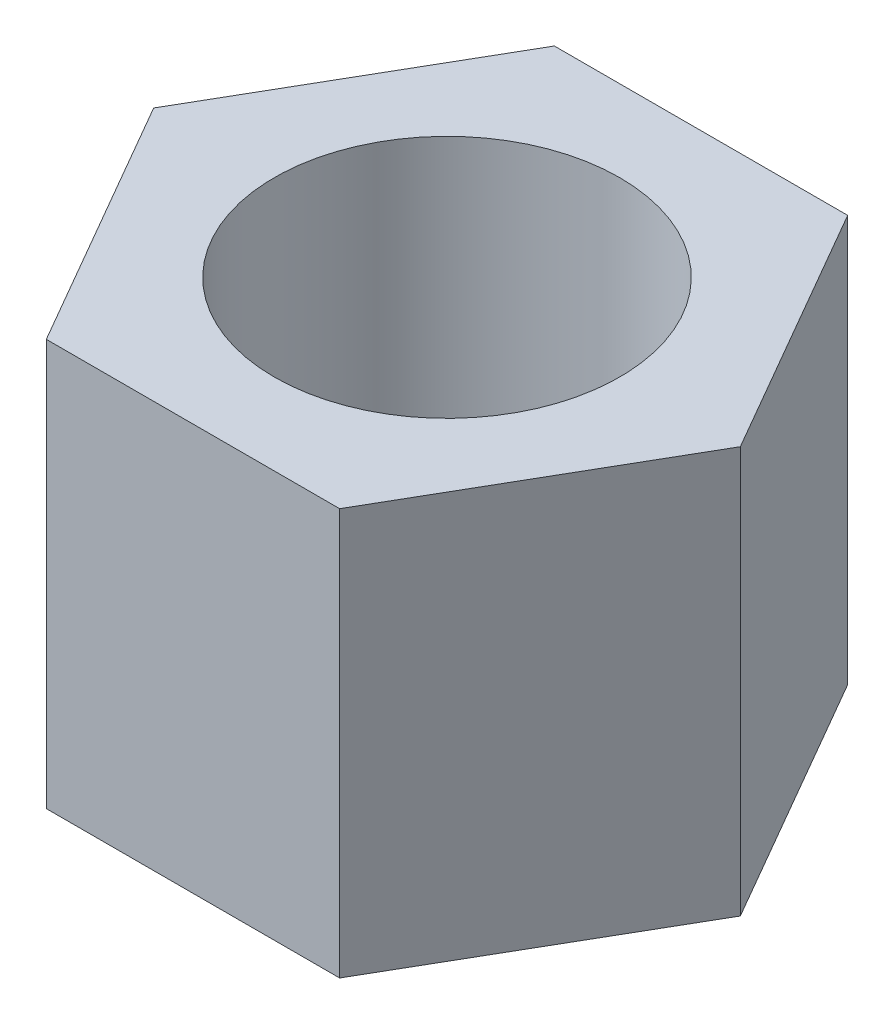
SolidWorks part; units mm, degrees
ref_plane "Front Plane" through (0, 0, 0) normal (0, 0, 1) x (1, 0, 0)
ref_plane "Top Plane" through (0, 0, 0) normal (0, 1, 0) x (1, 0, 0)
ref_plane "Right Plane" through (0, 0, 0) normal (1, 0, 0) x (0, 0, -1)
sketch "Sketch1" plane through (0, 0, 0) normal (0, 1, 0) x (1, 0, 0)
  line L1 (-2.8868, 0) -> (-1.4434, -2.5)
  line L2 (-1.4434, -2.5) -> (1.4434, -2.5)
  line L3 (1.4434, -2.5) -> (2.8868, 0)
  line L4 (2.8868, 0) -> (1.4434, 2.5)
  line L5 (1.4434, 2.5) -> (-1.4434, 2.5)
  line L6 (-1.4434, 2.5) -> (-2.8868, 0)
  circle A0 centre (0, 0) radius 1.7
  circle A1 centre (0, 0) radius 2.5 construction
  point P3 (0, 0)
  dimension "D1" = 3.4
  dimension "D2" = 5
extrude "Boss-Extrude1" add sketch "Sketch1" along normal mid plane 4
